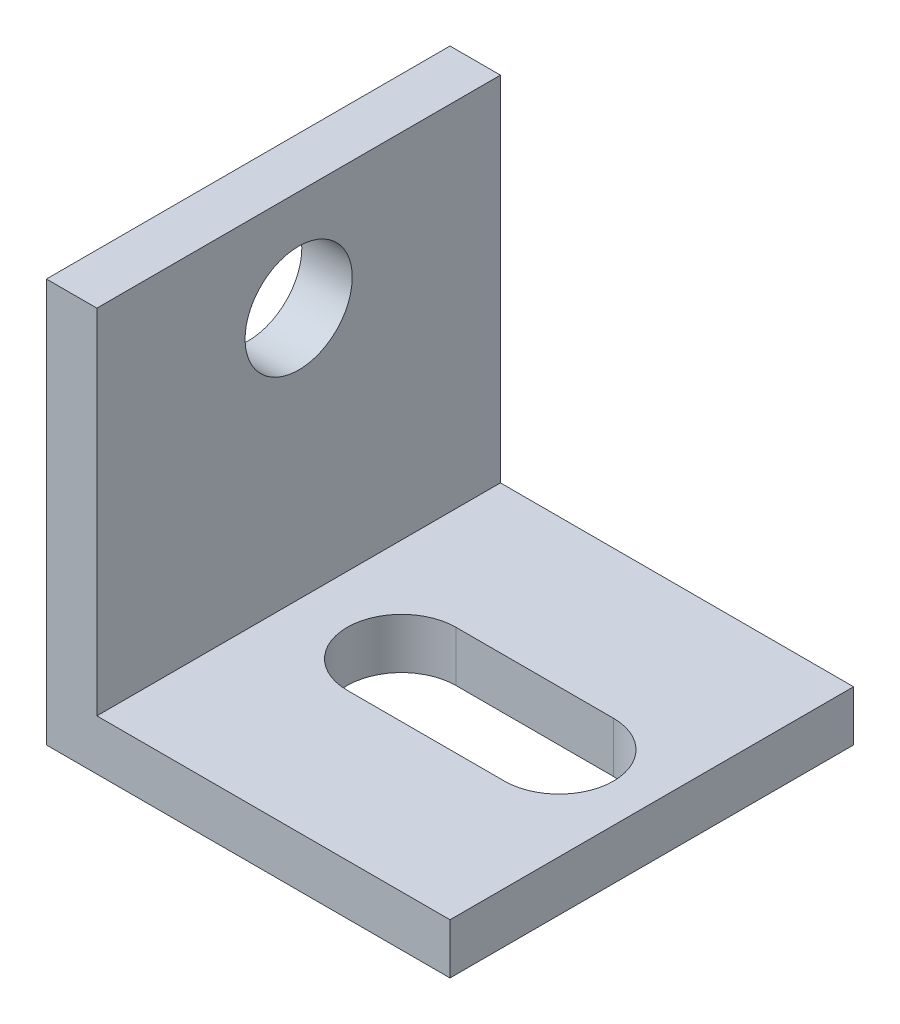
SolidWorks part; units mm, degrees
ref_plane "Front Plane" through (0, 0, 0) normal (0, 0, 1) x (1, 0, 0)
ref_plane "Top Plane" through (0, 0, 0) normal (0, 1, 0) x (1, 0, 0)
ref_plane "Right Plane" through (0, 0, 0) normal (1, 0, 0) x (0, 0, -1)
sketch "Sketch1" plane through (0, 0, 0) normal (0, 0, 1) x (1, 0, 0)
  line L0 (0, 0) -> (0, 25.4)
  line L1 (0, 0) -> (25.4, 0)
  line L2 (0, 25.4) -> (3.175, 25.4)
  line L3 (3.175, 25.4) -> (3.175, 3.175)
  line L4 (3.175, 3.175) -> (25.4, 3.175)
  line L5 (25.4, 3.175) -> (25.4, 0)
  dimension "D1" = 25.4
  dimension "D2" = 25.4
  dimension "D3" = 3.175
  dimension "D4" = 3.175
extrude "Boss-Extrude1" add sketch "Sketch1" along normal blind 25.4
sketch "Sketch2" plane through (0, 3.175, 0) normal (0, 1, 0) x (1, 0, 0)
  line L0 (0, -25.4) -> (0, 0) construction
  line L1 (25.4, 0) -> (3.175, 0) construction
  line L2 (9.652, -9.271) -> (19.558, -9.271)
  line L3 (9.652, -16.129) -> (19.558, -16.129)
  arc A0 (9.652, -9.271) -> (9.652, -16.129) centre (9.652, -12.7) ccw
  arc A2 (19.558, -16.129) -> (19.558, -9.271) centre (19.558, -12.7) ccw
  dimension "D3" = 6.858
  dimension "D5" = 3.429
  dimension "D1" = 9.652
  dimension "D2" = 12.7
  dimension "D4" = 19.558
extrude "Cut-Extrude1" cut sketch "Sketch2" against normal blind 25.4
sketch "Sketch3" plane through (3.175, 0, 0) normal (1, 0, 0) x (0, 0, -1)
  line L0 (-25.4, 25.4) -> (0, 25.4) construction
  line L1 (-25.4, 3.175) -> (-25.4, 25.4) construction
  circle A0 centre (-12.7, 19.05) radius 3.3734
  dimension "D3" = 6.7469
  dimension "D1" = 6.35
  dimension "D2" = 12.7
extrude "Cut-Extrude2" cut sketch "Sketch3" against normal blind 25.4
